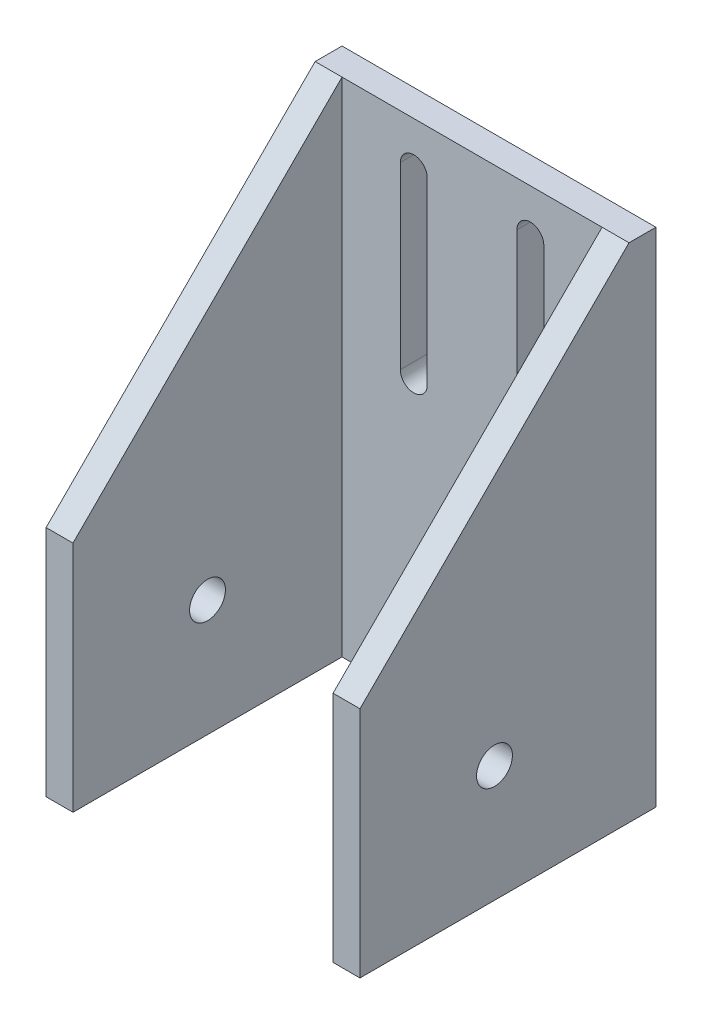
SolidWorks part; units mm, degrees
ref_plane "Front Plane" through (0, 0, 0) normal (0, 0, 1) x (1, 0, 0)
ref_plane "Top Plane" through (0, 0, 0) normal (0, 1, 0) x (1, 0, 0)
ref_plane "Right Plane" through (0, 0, 0) normal (1, 0, 0) x (0, 0, -1)
sketch "Sketch1" plane through (0, 0, 0) normal (0, 0, 1) x (1, 0, 0)
  line L0 (-6.5, 23) -> (-6.5, 3) construction
  line L1 (-17.5, 28) -> (17.5, 28)
  line L2 (-17.5, 28) -> (-17.5, -28)
  line L3 (-17.5, -28) -> (17.5, -28)
  line L4 (17.5, 28) -> (17.5, -28)
  line L5 (-17.5, 28) -> (17.5, -28) construction
  line L6 (-17.5, -28) -> (17.5, 28) construction
  line L7 (-5, 23) -> (-5, 3)
  line L8 (-8, 23) -> (-8, 3)
  line L9 (0, 28) -> (0, 0) construction
  line L10 (6.5, 23) -> (6.5, 3) construction
  line L11 (5, 23) -> (5, 3)
  line L12 (8, 23) -> (8, 3)
  arc A0 (-5, 23) -> (-8, 23) centre (-6.5, 23) ccw
  arc A1 (-8, 3) -> (-5, 3) centre (-6.5, 3) ccw
  arc A2 (5, 23) -> (8, 23) centre (6.5, 23) cw
  arc A3 (8, 3) -> (5, 3) centre (6.5, 3) cw
  point P0 (0, 0)
  point P8 (-6.5, 13)
  point P17 (6.5, 13)
  dimension "D3" = 5
  dimension "D1" = 35
  dimension "D2" = 56
  dimension "D4" = 10
  dimension "D5" = 3
  dimension "D6" = 20
extrude "Boss-Extrude1" add sketch "Sketch1" along normal blind 3
sketch "Sketch2" plane through (0, 0, 3) normal (0, 0, 1) x (1, 0, 0)
  line L5 (-17.5, 28) -> (-17.5, -28) construction
  line L11 (-17.5, -2) -> (-14.5, -2)
  line L13 (-17.5, -2) -> (-17.5, -28)
  line L14 (-17.5, -28) -> (-14.5, -28)
  line L15 (-14.5, -2) -> (-14.5, -28)
  line L16 (-17.5, -28) -> (17.5, -28) construction
  line L17 (0, 0) -> (0, -28) construction
  line L18 (-6.5, 1.5) -> (-6.5, -2) construction
  line L19 (-6.5, -2) -> (-14.5, -2) construction
  line L20 (-6.5, 24.5) -> (-6.5, 28) construction
  line L21 (17.5, 28) -> (-17.5, 28) construction
  line L22 (17.5, -28) -> (14.5, -28)
  line L23 (14.5, -2) -> (14.5, -28)
  line L24 (17.5, -2) -> (14.5, -2)
  line L25 (17.5, -2) -> (17.5, -28)
  arc A2 (-8, 3) -> (-5, 3) centre (-6.5, 3) ccw construction
  arc A3 (-5, 23) -> (-8, 23) centre (-6.5, 23) ccw construction
  dimension "D1" = 3
extrude "Boss-Extrude2" add sketch "Sketch2" along normal blind 30
sketch "Sketch4" plane through (14.5, 0, 0) normal (-1, 0, 0) x (0, 0, 1)
  line L0 (33, -15) -> (18, -15) construction
  line L1 (33, -2) -> (33, -28) construction
  line L2 (18, -15) -> (18, -2) construction
  line L3 (33, -2) -> (3, -2) construction
  circle A0 centre (18, -15) radius 2
  dimension "D1" = 4
extrude "Cut-Extrude1" cut sketch "Sketch4" against normal through all both and the other way through all
sketch "Sketch5" plane through (-17.5, 0, 0) normal (-1, 0, 0) x (0, 0, 1)
  line L0 (3, 28) -> (33, -2)
  line L1 (33, -2) -> (3, -2)
  line L2 (3, -2) -> (3, 28)
extrude "Boss-Extrude3" add sketch "Sketch5" against normal through all
sketch "Sketch6" plane through (0, 0, 33) normal (0, 0, 1) x (1, 0, 0)
  line L0 (17.5, 28) -> (-17.5, 28) construction
  line L1 (-14.5, -2) -> (14.5, -2)
  line L2 (-14.5, -2) -> (-14.5, 28)
  line L3 (-14.5, 28) -> (14.5, 28)
  line L4 (14.5, -2) -> (14.5, 28)
  line L5 (14.5, -2) -> (14.5, -28) construction
  point P7 (0, 0)
extrude "Cut-Extrude2" cut sketch "Sketch6" against normal up to surface (30 mm away) up to face at (0, -15, 3)
